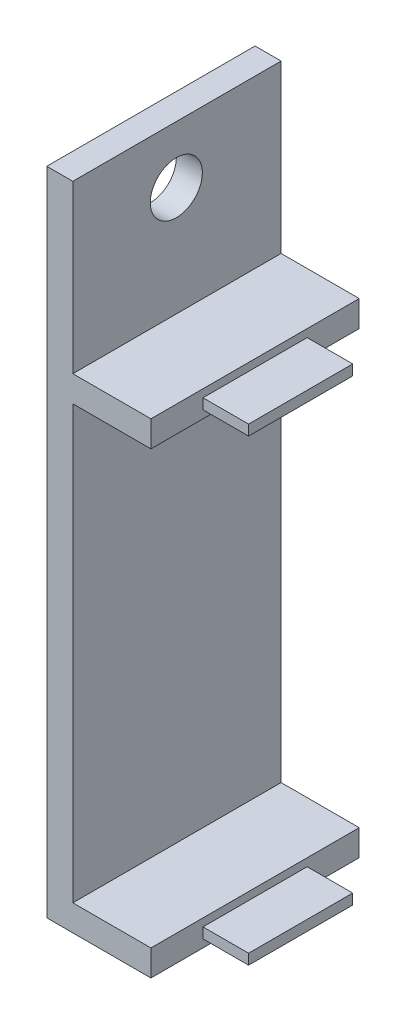
SolidWorks part; units mm, degrees
ref_plane "Front Plane" through (0, 0, 0) normal (0, 0, 1) x (1, 0, 0)
ref_plane "Top Plane" through (0, 0, 0) normal (0, 1, 0) x (1, 0, 0)
ref_plane "Right Plane" through (0, 0, 0) normal (1, 0, 0) x (0, 0, -1)
sketch "Sketch1" plane through (0, 0, 0) normal (0, 0, 1) x (1, 0, 0)
  line L0 (-22.4832, 11.6395) -> (-22.4832, -18.8404)
  line L1 (-22.4832, -18.8404) -> (-18.6732, -18.8404)
  line L2 (-18.6732, -18.8404) -> (-18.6732, -20.1105)
  line L3 (-18.6732, -20.1105) -> (-23.7532, -20.1105)
  line L4 (-23.7532, -20.1105) -> (-23.7532, 11.6395)
  line L5 (-23.7532, 11.6395) -> (-22.4832, 11.6395)
  dimension "D1" = 30.48
  dimension "D2" = 31.75
  dimension "D3" = 5.08
extrude "Boss-Extrude1" add sketch "Sketch1" along normal blind 10.16
sketch "Sketch6" plane through (-22.4832, 0, 0) normal (1, 0, 0) x (0, 0, -1)
  line L0 (-10.16, -18.8404) -> (-10.16, 2.2416) construction
  line L1 (-10.16, -18.8404) -> (-10.16, 11.6396) construction
  line L2 (-10.16, 2.2416) -> (0, 2.2416)
  line L3 (0, -18.8404) -> (0, 11.6396) construction
  line L4 (0, 2.2416) -> (0, 3.5116)
  line L5 (0, 3.5116) -> (-10.16, 3.5116)
  line L6 (-10.16, 3.5116) -> (-10.16, 2.2416)
  line L7 (-10.16, -18.8404) -> (0, -18.8404) construction
  dimension "D1" = 1.27
  dimension "D2" = 21.082
extrude "Boss-Extrude3" add sketch "Sketch6" along normal blind 3.81
sketch "Sketch14" plane through (-22.4832, 0, 0) normal (1, 0, 0) x (0, 0, -1)
  line L0 (-10.16, 11.6395) -> (0, 11.6395) construction
  point P0 (-5.1117, 8.8455)
  dimension "D1" = 2.794
sketch "Sketch23" plane through (-18.6732, 0, 0) normal (1, 0, 0) x (0, 0, -1)
  line L0 (-7.62, 3.1306) -> (-7.62, 2.6226)
  line L1 (-7.62, 2.6226) -> (-2.54, 2.6226)
  line L2 (-2.54, 2.6226) -> (-2.54, 3.1306)
  line L3 (-2.54, 3.1306) -> (-7.62, 3.1306)
  line L4 (-10.16, 2.2416) -> (0, 2.2416) construction
  line L5 (0, 3.5116) -> (-10.16, 3.5116) construction
  line L6 (0, 2.2416) -> (0, 3.5116) construction
  line L7 (-10.16, 3.5116) -> (-10.16, 2.2416) construction
  dimension "D1" = 0.381
  dimension "D2" = 0.381
  dimension "D3" = 2.54
  dimension "D4" = 2.54
extrude "Boss-Extrude4" add sketch "Sketch23" along normal blind 2.2225
sketch "Sketch25" plane through (-18.6732, 0, 0) normal (1, 0, 0) x (0, 0, -1)
  line L0 (-7.62, -19.2214) -> (-7.62, -19.7295)
  line L1 (-7.62, -19.7295) -> (-2.54, -19.7295)
  line L2 (-2.54, -19.7295) -> (-2.54, -19.2214)
  line L3 (-2.54, -19.2214) -> (-7.62, -19.2214)
  line L4 (-10.16, -18.8404) -> (0, -18.8404) construction
  line L5 (-10.16, -20.1105) -> (0, -20.1105) construction
  line L6 (0, -20.1105) -> (0, -18.8404) construction
  line L7 (-10.16, -20.1105) -> (-10.16, -18.8404) construction
  dimension "D1" = 0.381
  dimension "D2" = 0.381
  dimension "D3" = 2.54
  dimension "D4" = 2.54
extrude "Boss-Extrude5" add sketch "Sketch25" along normal blind 2.2225
sketch "Sketch26" plane through (-22.4832, 0, 0) normal (1, 0, 0) x (0, 0, -1)
  circle A0 centre (-5.1117, 8.8455) radius 1.27
extrude "Cut-Extrude1" cut sketch "Sketch26" against normal blind 2.2225
